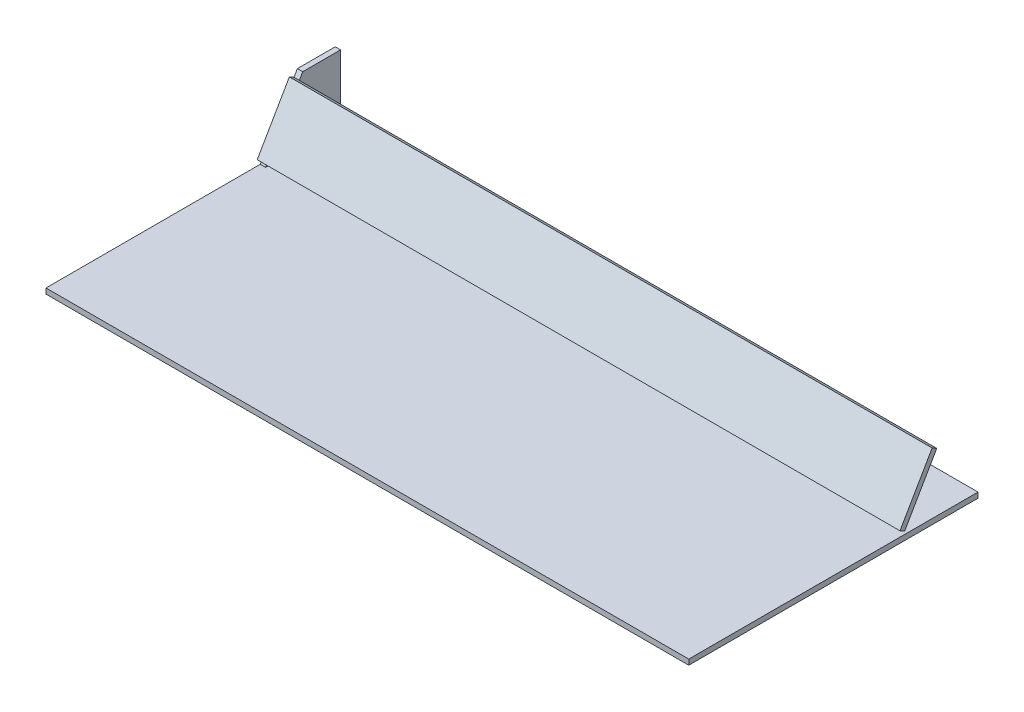
SolidWorks part; units mm, degrees
ref_plane "Front Plane" through (0, 0, 0) normal (0, 0, 1) x (1, 0, 0)
ref_plane "Top Plane" through (0, 0, 0) normal (0, 1, 0) x (1, 0, 0)
ref_plane "Right Plane" through (0, 0, 0) normal (1, 0, 0) x (0, 0, -1)
sketch "Sketch1" plane through (0, 0, 0) normal (0, 1, 0) x (1, 0, 0)
  line L0 (0, 0) -> (0, 135) construction
  line L1 (-300, 135) -> (300, 135)
  line L2 (-300, 135) -> (-300, -135)
  line L3 (-300, -135) -> (300, -135)
  line L4 (300, 135) -> (300, -135)
  line L5 (0, 0) -> (-300, 0) construction
  dimension "D1" = 270
  dimension "D2" = 600
extrude "Boss-Extrude1" add sketch "Sketch1" along normal blind 5
sketch "Sketch2" plane through (-300, 0, 0) normal (-1, 0, 0) x (0, 0, 1)
  line L0 (-99.641, 65) -> (-65, 5)
  line L1 (-135, 5) -> (-65, 5)
  line L2 (-135, 5) -> (-135, 65)
  line L3 (-135, 65) -> (-99.641, 65)
  line L5 (-135, 5) -> (135, 5) construction
  dimension "D1" = 60
  dimension "D2" = 120
  dimension "D3" = 200
extrude "Boss-Extrude2" add sketch "Sketch2" against normal blind 5 separate body
sketch "Sketch3" plane through (-300, 0, 0) normal (-1, 0, 0) x (0, 0, 1)
  line L0 (-65, 5) -> (-99.641, 65) construction
  line L1 (-96.5, 59.5596) -> (-66.5, 7.5981)
  line L2 (-66.5, 7.5981) -> (-62.1699, 10.0981)
  line L3 (-62.1699, 10.0981) -> (-92.1699, 62.0596)
  line L4 (-92.1699, 62.0596) -> (-96.5, 59.5596)
  dimension "D1" = 5
  dimension "D2" = 60
  dimension "D3" = 3
extrude "Boss-Extrude4" add sketch "Sketch3" against normal up to surface (600 mm away) separate body up to face at (300, 2.5, 0)
other "Save Bodies1"
